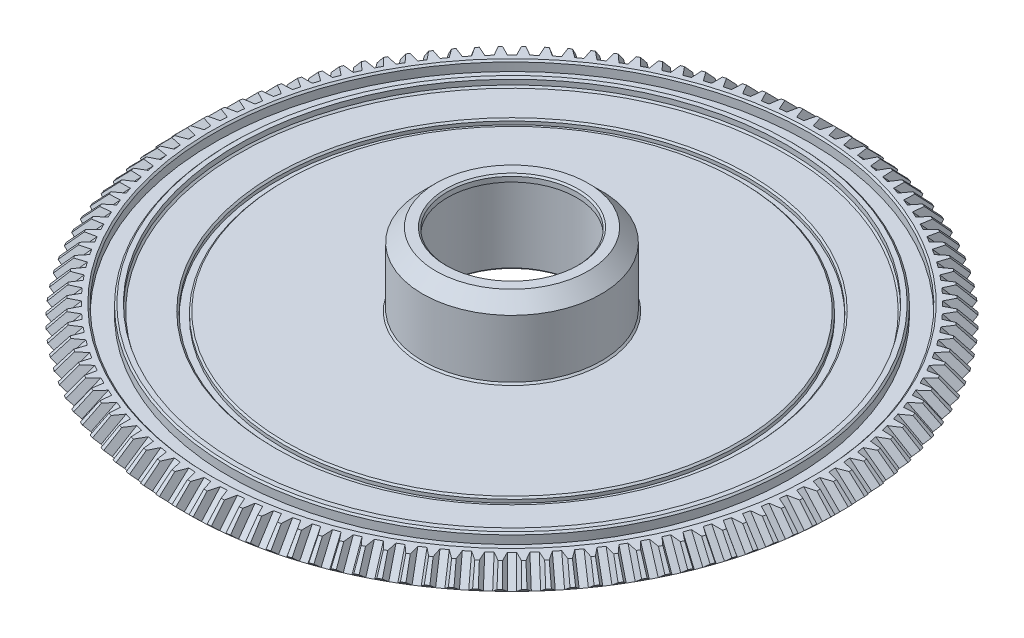
SolidWorks part; units mm, degrees
ref_plane "Front Plane" through (0, 0, 0) normal (0, 0, 1) x (1, 0, 0)
ref_plane "Top Plane" through (0, 0, 0) normal (0, 1, 0) x (1, 0, 0)
ref_plane "Right Plane" through (0, 0, 0) normal (1, 0, 0) x (0, 0, -1)
sketch "Sketch1" plane through (0, 0, 0) normal (0, 0, 1) x (1, 0, 0)
  line L2 (83, 4) -> (83, 6)
  line L3 (83, 6) -> (84.9, 6)
  line L4 (84.9, 6) -> (84.9, 3)
  line L5 (84.9, 3) -> (90.1, 3)
  line L6 (90.1, 3) -> (90.1, 6)
  line L7 (90.1, 6) -> (95.1, 6)
  line L8 (97.9887, 0) -> (21, 0)
  line L9 (21, 0) -> (21, 24)
  line L10 (0, 0) -> (0, 26) construction
  line L11 (27, 26) -> (27, 4)
  line L12 (27, 4) -> (68.9, 4)
  line L13 (21, 24) -> (19.5, 24)
  line L14 (19.5, 24) -> (19.5, 26)
  line L15 (19.5, 26) -> (27, 26)
  line L19 (71.1, 4) -> (83, 4)
  line L20 (68.9, 4) -> (68.9, 2.5)
  line L21 (68.9, 2.5) -> (71.1, 2.5)
  line L22 (71.1, 2.5) -> (71.1, 4)
  line L23 (95.1, 6) -> (99.5444, 1.5556)
  line L24 (99.5444, 1.5556) -> (97.9887, 0)
  line L25 (97.9887, 0) -> (91.9887, 6) construction
  point P11 (70, 2.5)
  dimension "D1" = 21
  dimension "D2" = 1.5
  dimension "D3" = 24
  dimension "D4" = 2
  dimension "D5" = 5.2
  dimension "D6" = 1.9
  dimension "D7" = 5
  dimension "D8" = 3
  dimension "D9" = 6
  dimension "D10" = 84.9
  dimension "D11" = 4
  dimension "D12" = 3
  dimension "D13" = 2.2
  dimension "D14" = 1.5
  dimension "D15" = 70
  dimension "D16" = 45
  dimension "D17" = 2.2
revolve "Revolve1" add sketch "Sketch1" angle 360 about L10
ref_plane "Plane1" through (0, 0, 0) normal (0, -0.7071, 0.7071) x (1, 0, 0)
sketch "Sketch2" plane through (0, 0, 0) normal (0, -0.7071, 0.7071) x (1, 0, 0)
  line L0 (0, 0) -> (0, 71.4885) construction
  line L1 (-2, 71.4743) -> (-1, 69.2849)
  line L2 (2, 71.4743) -> (1, 69.2849)
  ellipse E0 centre (0, 1.1) end of major axis (-99.5444, 1.1) minor radius 70.3885 construction
  ellipse E1 centre (0, 1.1) end of major axis (99.5444, 1.1) minor radius 70.3885 (2, 71.4743) -> (-2, 71.4743) ccw
  ellipse E2 centre (0, 0) end of major axis (-97.9887, 0) minor radius 69.2885 construction
  ellipse E3 centre (0, 0) end of major axis (-97.9887, 0) minor radius 69.2885 (1, 69.2849) -> (-1, 69.2849) ccw
  dimension "D1" = 4
  dimension "D2" = 2
extrude "Cut-Extrude1" cut sketch "Sketch2" along normal up to surface (69.2849 mm away)
pattern_circular "CirPattern1" count 120 over 360 of "Cut-Extrude1"
chamfer "Chamfer3" distance 4 angle 45 1 edges at (0, 26, -27)
chamfer "Chamfer4" distance 0.5 angle 45 9 edges at (0, 24, -21) (0, 26, -19.5) (0, 0, -21) (0, 4, -83) (0, 6, -90.1) (0, 6, -84.9) (0, 4, -71.1) (0, 4, -68.9) (0, 4, -27)
